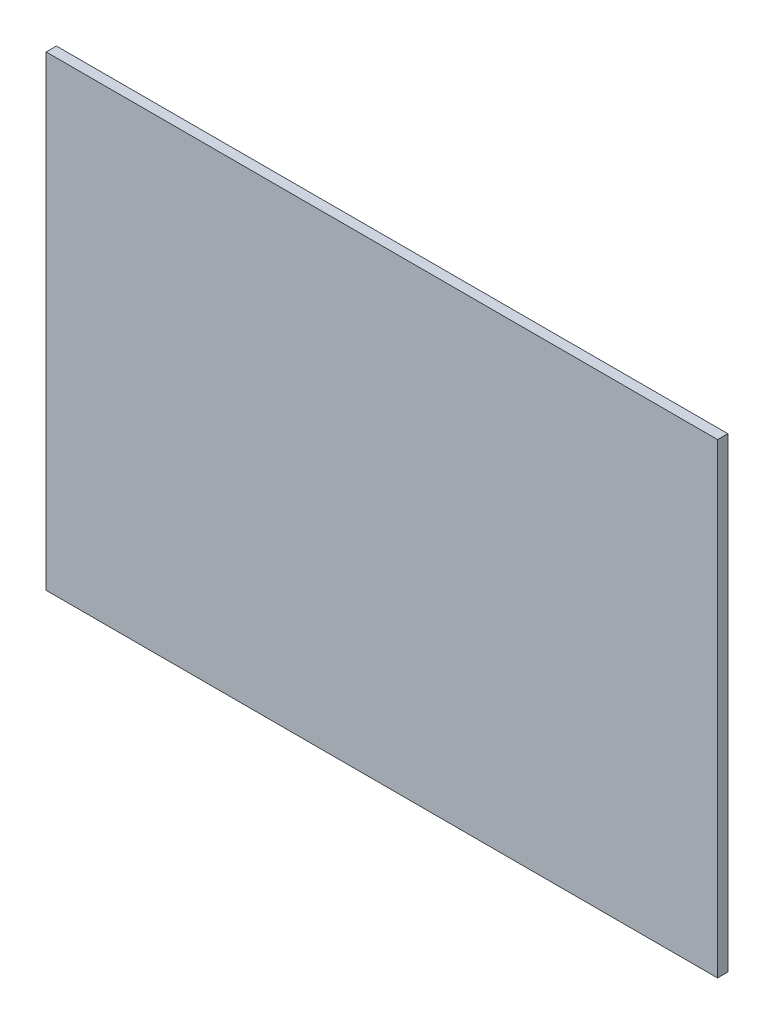
SolidWorks part; units mm, degrees
ref_plane "前视基准面" through (0, 0, 0) normal (0, 0, 1) x (1, 0, 0)
ref_plane "上视基准面" through (0, 0, 0) normal (0, 1, 0) x (1, 0, 0)
ref_plane "右视基准面" through (0, 0, 0) normal (1, 0, 0) x (0, 0, -1)
sketch "草图1" plane through (0, 0, 0) normal (0, 0, 1) x (1, 0, 0)
  line L1 (-25, 25) -> (47, 25)
  line L2 (-25, 25) -> (-25, -25)
  line L3 (-25, -25) -> (47, -25)
  line L4 (47, 25) -> (47, -25)
  circle A0 centre (0, 0) radius 25 construction
  dimension "D1" = 50
  dimension "D2" = 72
  dimension "D3" = 50
extrude "凸台-拉伸1" add sketch "草图1" along normal blind 1.1
